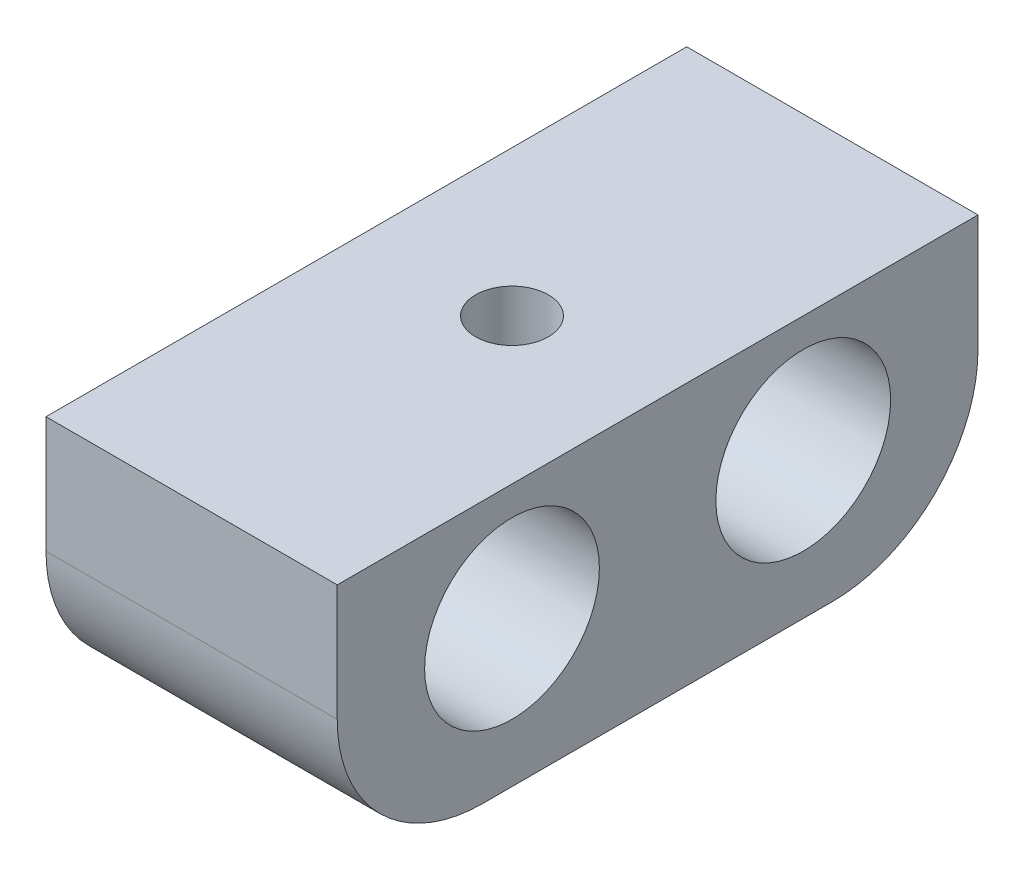
SolidWorks part; units mm, degrees
material "7050-T73510"
ref_plane "Front Plane" through (0, 0, 0) normal (0, 0, 1) x (1, 0, 0)
ref_plane "Top Plane" through (0, 0, 0) normal (0, 1, 0) x (1, 0, 0)
ref_plane "Right Plane" through (0, 0, 0) normal (1, 0, 0) x (0, 0, -1)
sketch "Sketch1" plane through (0, 0, 0) normal (1, 0, 0) x (0, 0, -1)
  line L0 (-6, 4) -> (-6, -5)
  line L1 (-6, -5) -> (16, -5)
  line L2 (16, -5) -> (16, 4)
  line L3 (16, 4) -> (-6, 4)
  circle A0 centre (0, 0) radius 3
  circle A1 centre (10, 0) radius 3
  dimension "D1" = 6
  dimension "D2" = 6
  dimension "D3" = 10
  dimension "D4" = 4
  dimension "D5" = 5
  dimension "D6" = 6
  dimension "D7" = 6
extrude "Boss-Extrude1" add sketch "Sketch1" along normal blind 10
fillet "Fillet1" radius 5 2 edges at (5, -5, -16) (5, -5, 6)
hole_wizard "M3 Tapped Hole1" positions "Sketch3" profile "Sketch2" tap size "M3" standard "ISO"
sketch "Sketch3" plane through (0, 4, 0) normal (0, 1, 0) x (1, 0, 0)
  line L0 (10, -6) -> (0, -6) construction
  line L1 (5, 16) -> (5, -6) construction
  line L2 (10, 16) -> (0, 16) construction
  point P0 (5, 5)
sketch "Sketch2" plane through (5, 4, -5) normal (1, 0, 0) x (0, 0, 1)
  line L0 (0, 0) -> (0, 8.2511)
  line L1 (0, 8.2511) -> (1.25, 7.5)
  line L2 (1.25, 7.5) -> (1.25, 0)
  line L5 (1.25, 0) -> (0, 0)
  line L10 (0, 8.2511) -> (-1.25, 7.5) construction
  line L11 (0, -6.35) -> (0, 107.95) construction
  dimension "Tap Drill Dia." = 2.5
  dimension "Tap Drill Depth" = 7.5
  dimension "Drill Angle" = 118
cosmetic thread "Hole Thread1" parameters "D1"=6, "D2"=3
